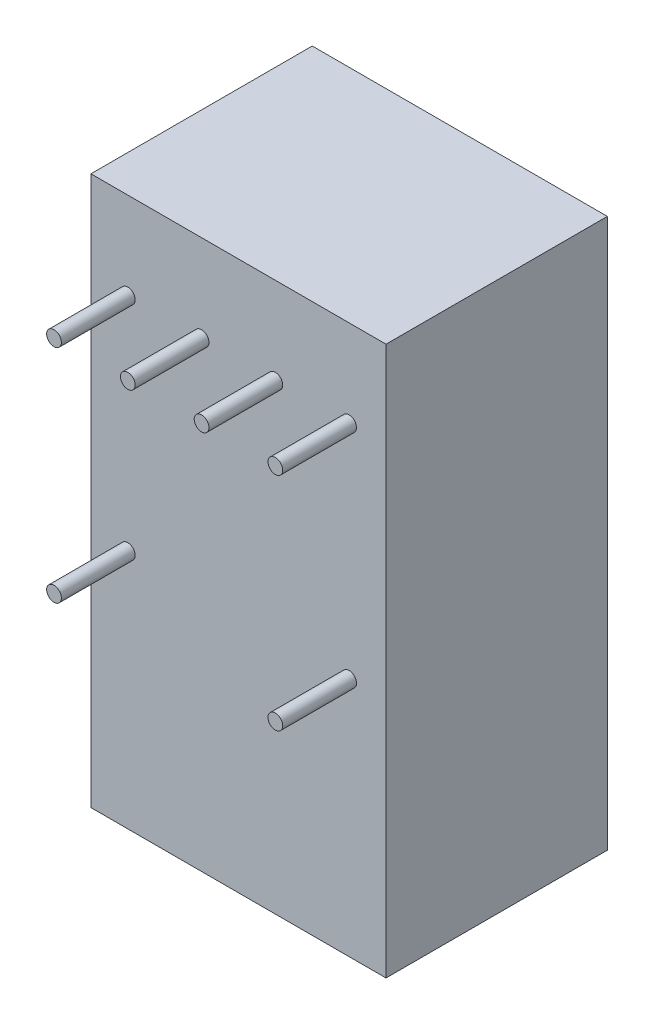
SolidWorks part; units mm, degrees
ref_plane "Front" through (0, 0, 0) normal (0, 0, 1) x (1, 0, 0)
ref_plane "Top" through (0, 0, 0) normal (0, 1, 0) x (1, 0, 0)
ref_plane "Right" through (0, 0, 0) normal (1, 0, 0) x (0, 0, -1)
sketch "Sketch1" plane through (0, 0, 0) normal (0, 0, 1) x (1, 0, 0)
  circle A0 centre (0, 0) radius 0.254
  circle A1 centre (2.54, 0) radius 0.254
  circle A2 centre (5.08, 0) radius 0.254
  circle A3 centre (7.62, 0) radius 0.254
  circle A4 centre (0, -7.62) radius 0.254
  circle A5 centre (7.62, -7.62) radius 0.254
  dimension "D1" = 0.508
  dimension "D2" = 0.508
  dimension "D3" = 0.508
  dimension "D4" = 0.508
  dimension "D5" = 0.508
  dimension "D6" = 0.508
  dimension "D7" = 2.54
  dimension "D8" = 2.54
  dimension "D9" = 2.54
  dimension "D10" = 7.62
extrude "Extrude1" add sketch "Sketch1" along normal blind 2.54
sketch "Sketch2" plane through (0, 0, 0) normal (0, 0, -1) x (-1, 0, 0)
  line L1 (-8.89, 2.9972) -> (1.27, 2.9972)
  line L2 (-8.89, 2.9972) -> (-8.89, -15.9004)
  line L3 (-8.89, -15.9004) -> (1.27, -15.9004)
  line L4 (1.27, 2.9972) -> (1.27, -15.9004)
  dimension "D1" = 10.16
  dimension "D2" = 18.8976
  dimension "D3" = 1.27
  dimension "D4" = 2.9972
extrude "Extrude2" add sketch "Sketch2" along normal blind 7.62
